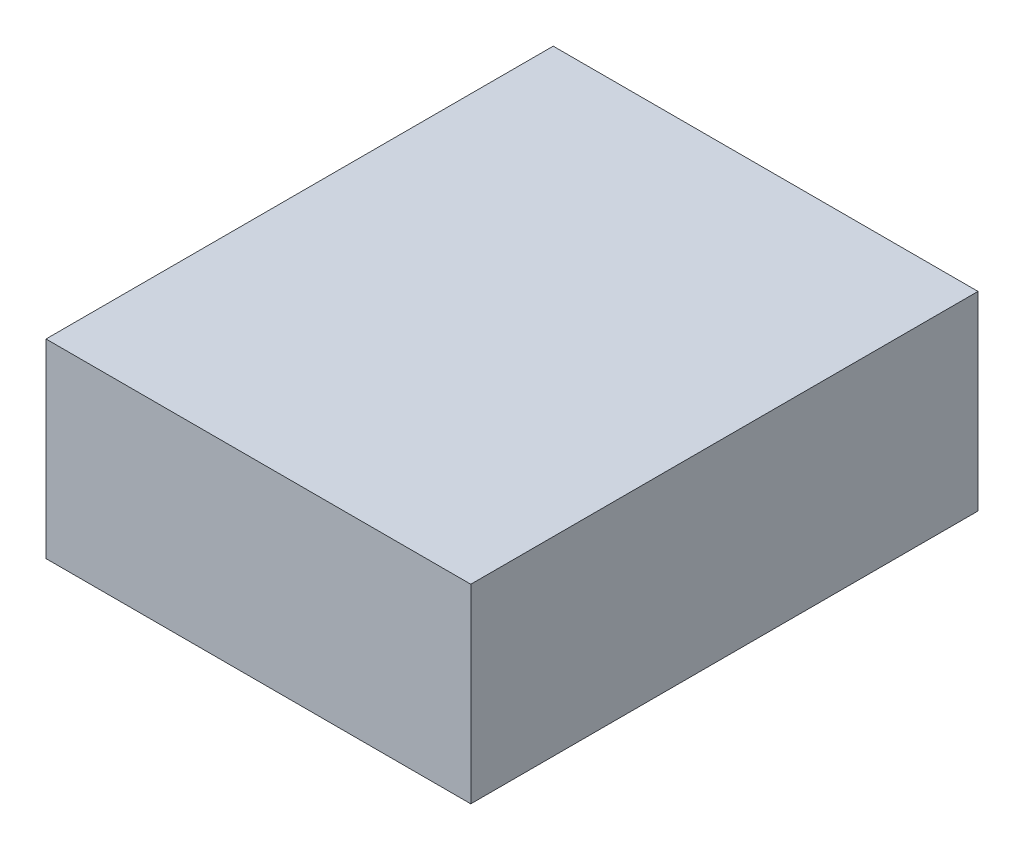
SolidWorks part; units mm, degrees
material "Custom Plastic"
ref_plane "Front Plane" through (0, 0, 0) normal (0, 0, 1) x (1, 0, 0)
ref_plane "Top Plane" through (0, 0, 0) normal (0, 1, 0) x (1, 0, 0)
ref_plane "Right Plane" through (0, 0, 0) normal (1, 0, 0) x (0, 0, -1)
sketch "Sketch1" plane through (0, 0, 0) normal (0, 1, 0) x (1, 0, 0)
  line L1 (-8.509, 10.16) -> (8.509, 10.16)
  line L2 (-8.509, 10.16) -> (-8.509, -10.16)
  line L3 (-8.509, -10.16) -> (8.509, -10.16)
  line L4 (8.509, 10.16) -> (8.509, -10.16)
  line L5 (-8.509, 10.16) -> (8.509, -10.16) construction
  line L6 (-8.509, -10.16) -> (8.509, 10.16) construction
  point P0 (0, 0)
extrude "Extrude1" add sketch "Sketch1" along normal blind 7.62
